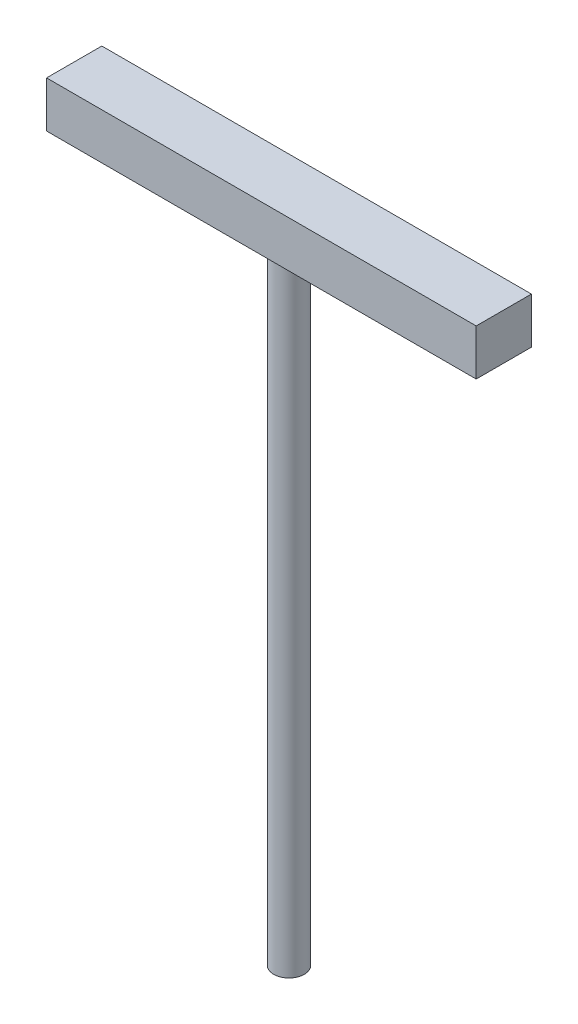
SolidWorks part; units mm, degrees
ref_plane "Front Plane" through (0, 0, 0) normal (0, 0, 1) x (1, 0, 0)
ref_plane "Top Plane" through (0, 0, 0) normal (0, 1, 0) x (1, 0, 0)
ref_plane "Right Plane" through (0, 0, 0) normal (1, 0, 0) x (0, 0, -1)
sketch "Sketch1" plane through (0, 0, 0) normal (1, 0, 0) x (0, 0, -1)
  line L1 (5.715, 4.7625) -> (-5.715, 4.7625)
  line L2 (5.715, 4.7625) -> (5.715, -4.7625)
  line L3 (5.715, -4.7625) -> (-5.715, -4.7625)
  line L4 (-5.715, 4.7625) -> (-5.715, -4.7625)
  line L5 (5.715, 4.7625) -> (-5.715, -4.7625) construction
  line L6 (5.715, -4.7625) -> (-5.715, 4.7625) construction
  point P0 (0, 0)
  dimension "D1" = 11.43
  dimension "D2" = 9.525
extrude "Boss-Extrude1" add sketch "Sketch1" along normal blind 88.9
sketch "Sketch2" plane through (0, -4.7625, 0) normal (0, -1, 0) x (1, 0, 0)
  line L0 (88.9, 5.715) -> (88.9, -5.715) construction
  line L1 (88.9, 5.715) -> (0, 5.715) construction
  circle A0 centre (44.45, 0) radius 3.175
  point P4 (88.9, 0)
  point P8 (44.45, 5.715)
  dimension "D1" = 6.35
extrude "Boss-Extrude2" add sketch "Sketch2" along normal blind 130.175
